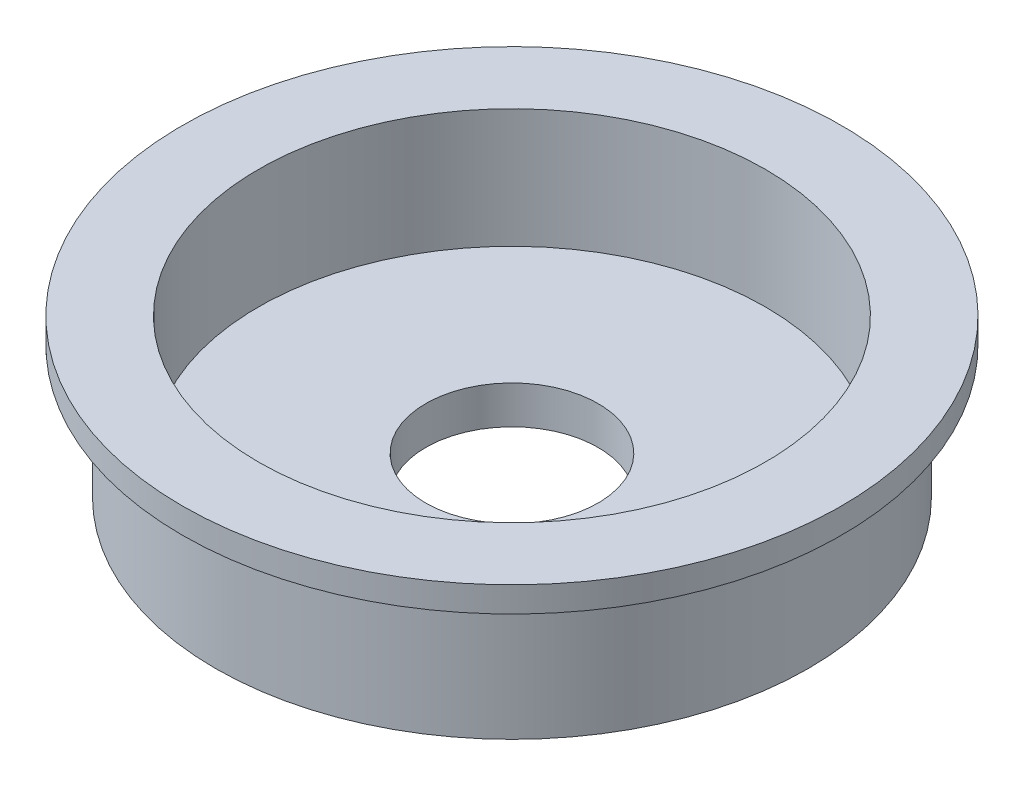
SolidWorks part; units mm, degrees
ref_plane "Front Plane" through (0, 0, 0) normal (0, 0, 1) x (1, 0, 0)
ref_plane "Top Plane" through (0, 0, 0) normal (0, 1, 0) x (1, 0, 0)
ref_plane "Right Plane" through (0, 0, 0) normal (1, 0, 0) x (0, 0, -1)
sketch "Sketch1" plane through (0, 0, 0) normal (0, 1, 0) x (1, 0, 0)
  circle A0 centre (0, 0) radius 14.859
  circle A1 centre (0, 0) radius 4.318
  dimension "D1" = 8.636
  dimension "D2" = 29.718
extrude "Boss-Extrude1" add sketch "Sketch1" along normal blind 6.604
sketch "Sketch2" plane through (0, 6.604, 0) normal (0, 1, 0) x (1, 0, 0)
  circle A0 centre (0, 0) radius 4.318
  circle A1 centre (0, 0) radius 16.51
  circle A2 centre (0, 0) radius 4.318 construction
  dimension "D1" = 33.02
extrude "Boss-Extrude2" add sketch "Sketch2" along normal blind 1.27
sketch "Sketch3" plane through (0, 7.874, 0) normal (0, 1, 0) x (1, 0, 0)
  circle A0 centre (0, 0) radius 12.7
  dimension "D1" = 25.4
extrude "Cut-Extrude1" cut sketch "Sketch3" against normal blind 5.969
